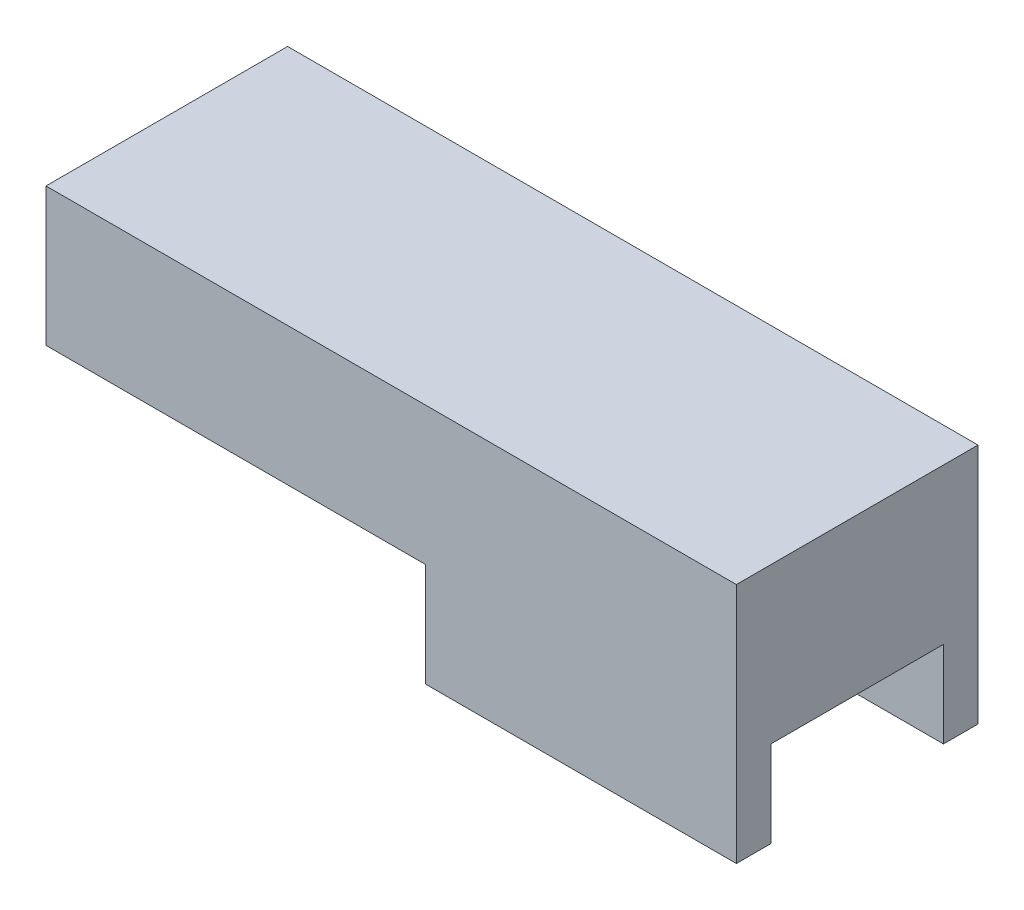
SolidWorks part; units mm, degrees
ref_plane "前视基准面" through (0, 0, 0) normal (0, 0, 1) x (1, 0, 0)
ref_plane "上视基准面" through (0, 0, 0) normal (0, 1, 0) x (1, 0, 0)
ref_plane "右视基准面" through (0, 0, 0) normal (1, 0, 0) x (0, 0, -1)
sketch "草图1" plane through (0, 0, 0) normal (0, 0, 1) x (1, 0, 0)
  line L0 (-42.562, 30.9509) -> (157.438, 30.9509)
  line L1 (157.438, 30.9509) -> (157.438, -39.0491)
  line L2 (157.438, -39.0491) -> (67.438, -39.0491)
  line L3 (67.438, -39.0491) -> (67.438, -9.0491)
  line L4 (67.438, -9.0491) -> (-42.562, -9.0491)
  line L5 (-42.562, -9.0491) -> (-42.562, 30.9509)
  dimension "D1" = 40
  dimension "D2" = 200
  dimension "D3" = 110
  dimension "D4" = 70
extrude "凸台-拉伸2" add sketch "草图1" along normal blind 70
sketch "草图3" plane through (67.438, 0, 0) normal (-1, 0, 0) x (0, 0, 1)
  line L0 (10, -39.0491) -> (10, -14.0491)
  line L1 (70, -39.0491) -> (0, -39.0491) construction
  line L2 (10, -14.0491) -> (60, -14.0491)
  line L3 (60, -14.0491) -> (60, -39.0491)
  line L4 (60, -39.0491) -> (10, -39.0491)
  line L5 (0, -9.0491) -> (0, -39.0491) construction
  dimension "D1" = 50
  dimension "D2" = 25
  dimension "D3" = 10
extrude "切除-拉伸3" cut sketch "草图3" against normal through all
